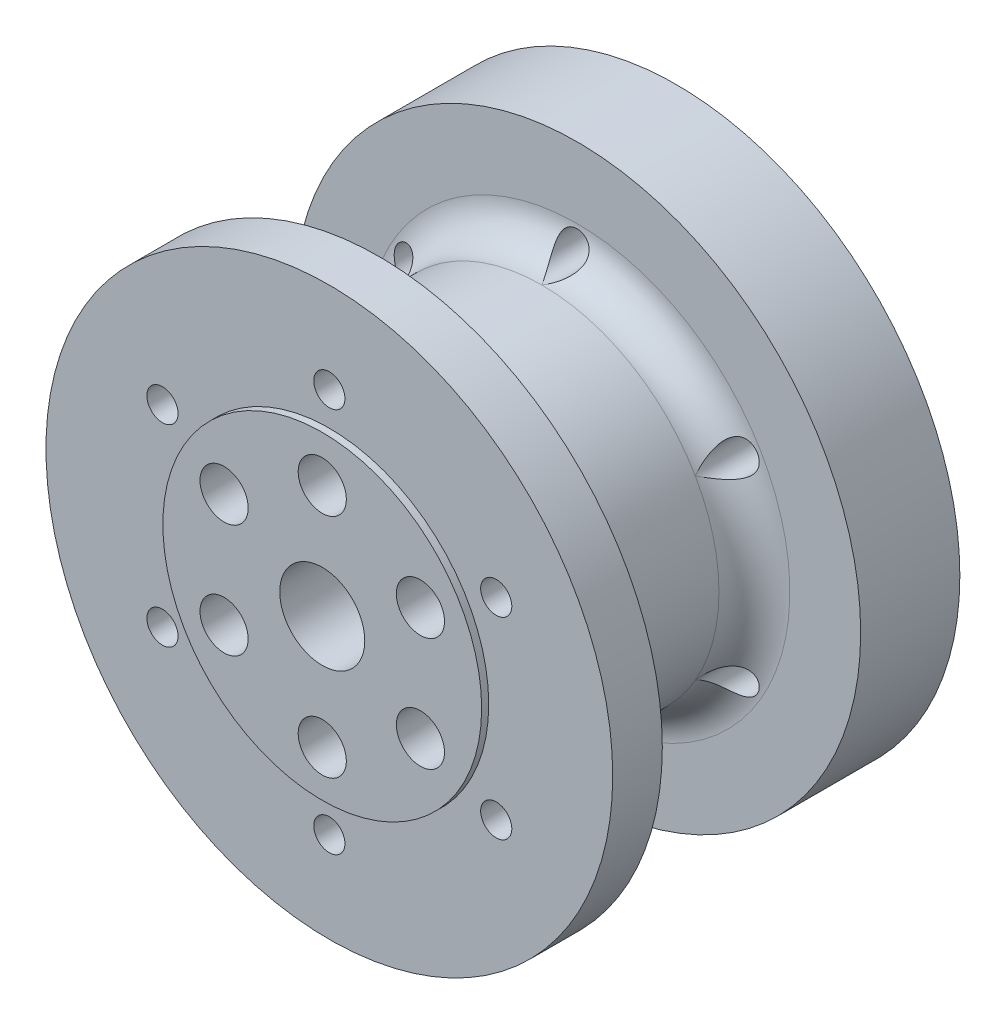
SolidWorks part; units mm, degrees
material "Nylon - impressão"
ref_plane "Plano frontal" through (0, 0, 0) normal (0, 0, 1) x (1, 0, 0)
ref_plane "Plano superior" through (0, 0, 0) normal (0, 1, 0) x (1, 0, 0)
ref_plane "Plano direito" through (0, 0, 0) normal (1, 0, 0) x (0, 0, -1)
sketch "Esboço1" plane through (0, 0, 0) normal (1, 0, 0) x (0, 0, -1)
  line L0 (1.5, 11.25) -> (1.5, 20)
  line L1 (1.5, 20) -> (5, 20)
  line L2 (5, 20) -> (5, 12.5)
  line L3 (5, 12.5) -> (19, 12.5)
  line L4 (19, 12.5) -> (19, 20)
  line L5 (19, 20) -> (27, 20)
  line L6 (27, 20) -> (27, 3)
  line L9 (27, 3) -> (0, 3)
  line L10 (0, 3) -> (0, 11.25)
  line L11 (0, 11.25) -> (1.5, 11.25)
  line L12 (0, 0) -> (24.3309, 0) construction
  line L14 (0, 11.25) -> (-3, 11.25) construction
  line L15 (0, 11.25) -> (0, 3) construction
  line L16 (0, 3) -> (-3, 3) construction
  line L17 (-3, 11.25) -> (-3, 3) construction
  dimension "D1" = 25
  dimension "D2" = 6
  dimension "D3" = 14
  dimension "D4" = 22.5
  dimension "D5" = 30
  dimension "D6" = 5
  dimension "D7" = 1.5
  dimension "D8" = 3
  dimension "D9" = 40
revolve "Revolução1" add sketch "Esboço1" angle 360 about L12
sketch "Esboço2" plane through (0, 0, -27) normal (0, 0, -1) x (-1, 0, 0)
  circle A0 centre (0, 0) radius 8 construction
  circle A1 centre (0, 8) radius 1.6
  circle A2 centre (6.9282, 4) radius 1.6
  circle A3 centre (6.9282, -4) radius 1.6
  circle A4 centre (0, -8) radius 1.6
  circle A5 centre (-6.9282, -4) radius 1.6
  circle A6 centre (-6.9282, 4) radius 1.6
  point P17 (0, 0)
  dimension "D1" = 16
  dimension "D2" = 3.2
  dimension "D3" = 6
extrude "Corte-extrusão1" cut sketch "Esboço2" against normal through all
hole_wizard "Rebaixo para SHCS M31" positions "Esboço3" profile "Esboço4" counterbore size "M3" standard "Ansi Metric" end condition through all
sketch "Esboço3" plane through (0, 0, -27) normal (0, 0, -1) x (-1, 0, 0)
  point P0 (0, 8)
  point P3 (-6.9282, 4)
  point P6 (-6.9282, -4)
  point P9 (0, -8)
  point P12 (6.9282, -4)
  point P15 (6.9282, 4)
sketch "Esboço4" plane through (0, 8, -27) normal (1, 0, 0) x (0, 1, 0)
  line L0 (0, 0) -> (0, 27)
  line L1 (0, 27) -> (1.7, 27)
  line L3 (1.7, 27) -> (1.7, 4)
  line L4 (3.25, 4) -> (1.7, 4)
  line L5 (3.25, 4) -> (3.25, 0.025)
  line L6 (3.25, 0.025) -> (3.275, 0)
  line L7 (3.275, 0) -> (0, 0)
  line L8 (-3.25, 0.025) -> (-3.275, 0) construction
  line L11 (0, -6.35) -> (0, 107.95) construction
  dimension "Thru Hole Dia." = 3.4
  dimension "Thru Hole Depth" = 27
  dimension "C'Bore Dia." = 6.5
  dimension "C'Bore Depth" = 4
  dimension "Near C'Sink Dia." = 6.55
  dimension "Near C'Sink Angle" = 90
sketch "Esboço5" plane through (0, 0, -27) normal (0, 0, -1) x (-1, 0, 0)
  circle A0 centre (0, 0) radius 11.275
extrude "Corte-extrusão2" cut sketch "Esboço5" against normal up to surface (4 mm away) up to face at (5.2282, 4, -23)
fillet "Filete1" radius 2.5 2 edges at (12.5, 0, -19) (12.5, 0, -5)
sketch "Esboço6" plane through (0, 0, -27) normal (0, 0, -1) x (-1, 0, 0)
  line L0 (0, -13.6) -> (0, 0) construction
  circle A0 centre (0, 0) radius 12.5 construction
  circle A1 centre (0, 0) radius 12.5 construction
  circle A2 centre (0, -13.6) radius 1.1
  circle A3 centre (-11.7779, -6.8) radius 1.1
  circle A4 centre (-11.7779, 6.8) radius 1.1
  circle A5 centre (0, 13.6) radius 1.1
  circle A6 centre (11.7779, 6.8) radius 1.1
  circle A7 centre (11.7779, -6.8) radius 1.1
  point P22 (0, 0)
  dimension "D1" = 2.2
  dimension "D2" = 6
extrude "Corte-extrusão3" cut sketch "Esboço6" against normal through all both and the other way through all
sketch "Esboço7" plane through (0, 0, -27) normal (0, 0, -1) x (-1, 0, 0)
  circle A0 centre (0, 0) radius 16.5
  dimension "D1" = 33
extrude "Corte-extrusão4" cut sketch "Esboço7" against normal up to surface (4 mm away) up to face at (-8.6282, 4, -23)
sketch "Esboço10" plane through (0, 0, -23) normal (0, 0, -1) x (-1, 0, 0)
  circle A0 centre (0, 0) radius 3 construction
  circle A1 centre (0, 0) radius 3
  circle A2 centre (0, 0) radius 5
  circle M7 centre (0, 0) radius 3
  dimension "D1" = 10
extrude "Ressalto-extrusão3" add sketch "Esboço10" along normal offset from surface (7 mm away) 3 contours A2 M7 up to face at (-16.5, 0, -27) offset beyond the face yes
sketch "Esboço11" plane through (0, 0, -27) normal (0, 0, -1) x (-1, 0, 0)
  circle A0 centre (0, 0) radius 16.5 construction
  circle A1 centre (0, 0) radius 20
  circle A2 centre (0, 0) radius 20
  circle A3 centre (0, 0) radius 16.5
  dimension "D1" = 0
extrude "Corte-extrusão6" cut sketch "Esboço11" against normal blind 1
sketch "Esboço12" plane through (0, 0, 0) normal (0, 0, 1) x (1, 0, 0)
  circle A1 centre (0, 0) radius 11.25
  circle A2 centre (0, 0) radius 11.25
  dimension "D1" = 0
extrude "Corte-extrusão7" cut sketch "Esboço12" against normal blind 1
